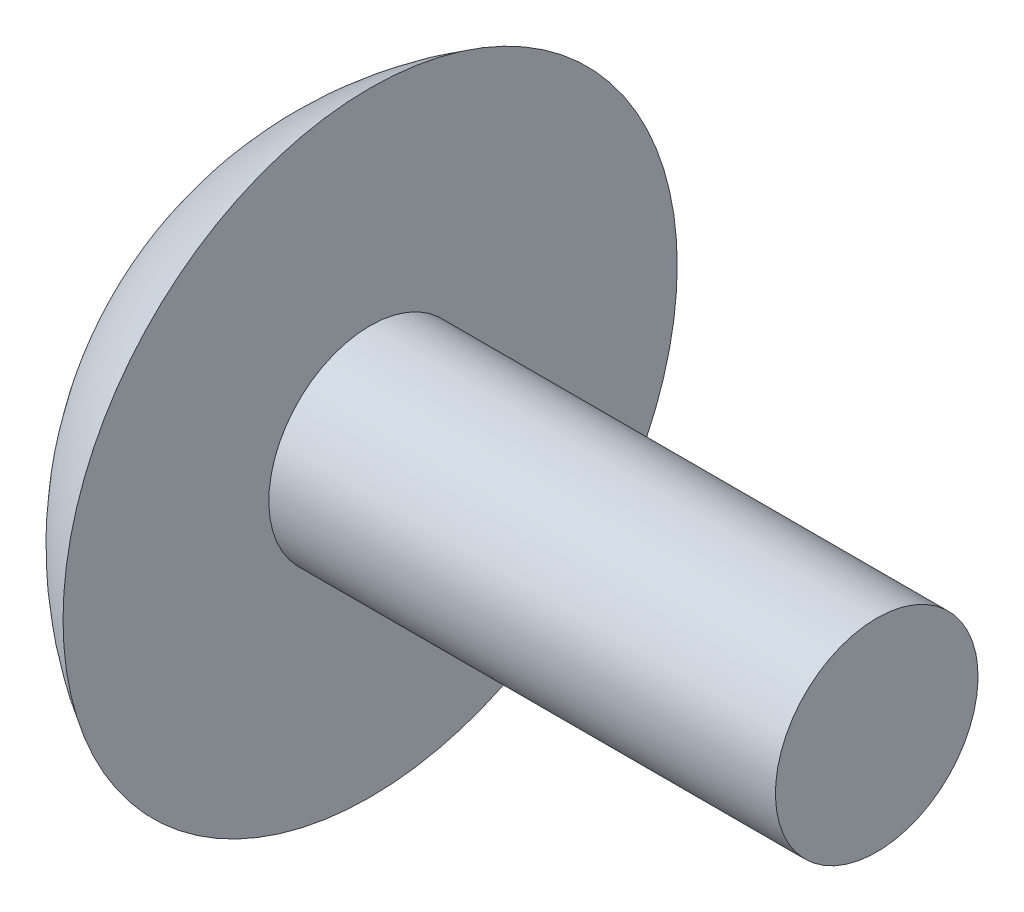
SolidWorks part; units mm, degrees
ref_plane "Plan de face" through (0, 0, 0) normal (0, 0, 1) x (1, 0, 0)
ref_plane "Plan de dessus" through (0, 0, 0) normal (0, 1, 0) x (1, 0, 0)
ref_plane "Plan de droite" through (0, 0, 0) normal (1, 0, 0) x (0, 0, -1)
sketch "Esquisse5" plane through (0, 0, 0) normal (0, 0, 1) x (1, 0, 0)
  line L0 (0, 0) -> (-13.5, 0)
  line L1 (0, 0) -> (0, -2)
  line L2 (0, -2) -> (-10, -2)
  line L3 (-10, -2) -> (-10, -6.0622)
  arc A0 (-13.5, 0) -> (-10, -6.0622) centre (-6.5, 0) ccw
  dimension "D1" = 7
  dimension "D2" = 13.5
  dimension "D3" = 2
  dimension "D4" = 10
revolve "Révolution2" add sketch "Esquisse5" angle 360 about L0
